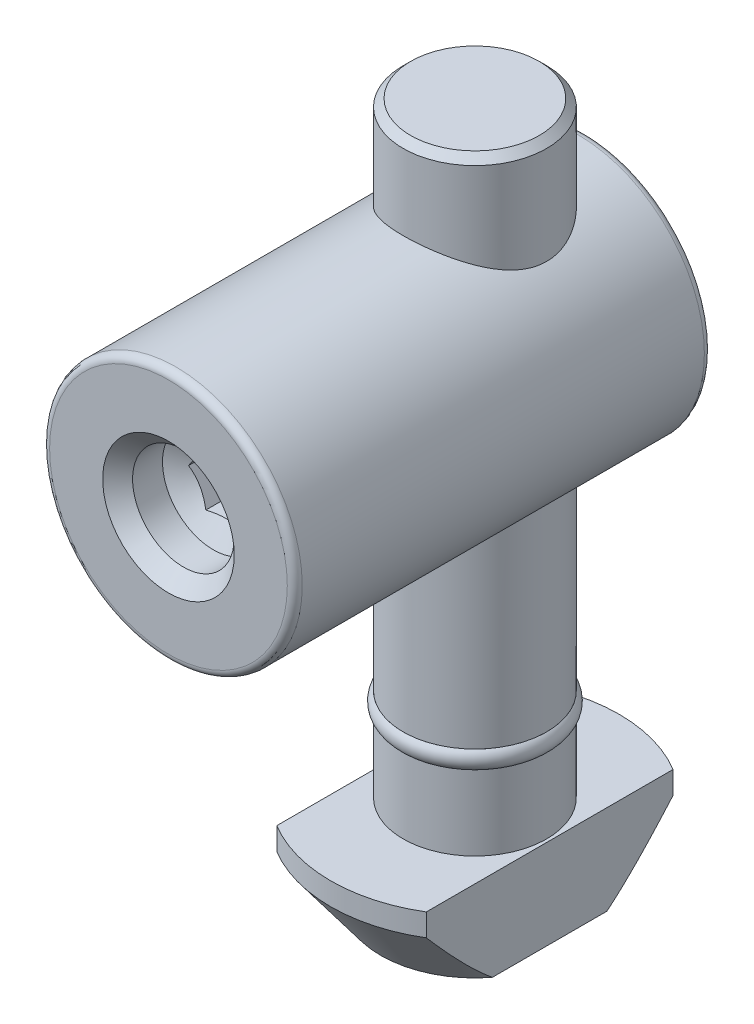
SolidWorks part; units mm, degrees
ref_plane "Спереди" through (0, 0, 0) normal (0, 0, 1) x (1, 0, 0)
ref_plane "Сверху" through (0, 0, 0) normal (0, 1, 0) x (1, 0, 0)
ref_plane "Справа" through (0, 0, 0) normal (1, 0, 0) x (0, 0, -1)
sketch "Эскиз3" plane through (0, 0, 0) normal (0, 0, 1) x (1, 0, 0)
  line L0 (0, 0) -> (-4.8, 0)
  line L1 (-4.8, 0) -> (-4.8, -34.3)
  line L2 (-4.8, -34.3) -> (-4.3, -34.3)
  line L3 (-4.3, -34.3) -> (-4.3, -35.5)
  line L4 (-4.3, -35.5) -> (-4.8, -35.5)
  line L5 (-4.8, -35.5) -> (-4.8, -40.5)
  line L7 (0, -46.5) -> (0, 0)
  line L8 (0, 0) -> (0, 5.384) construction
  line L9 (-4.8, -40.5) -> (-9.65, -40.5)
  line L10 (-9.65, -40.5) -> (-9.65, -42)
  line L11 (-9.65, -42) -> (-6.3, -46.5)
  line L12 (-6.3, -46.5) -> (0, -46.5)
  point P3 (0, -29.8286)
  point P9 (-4.2202, -32)
  dimension "D1" = 9.6
  dimension "D2" = 1.2
  dimension "D3" = 46.5
  dimension "D4" = 0.5
  dimension "D5" = 5
  dimension "D6" = 6
  dimension "D7" = 1.5
  dimension "D8" = 1.5
  dimension "D9" = 19.3
revolve "Повернуть1" add sketch "Эскиз3" angle 360 about L8
sketch "Эскиз6" plane through (0, -46.5, 0) normal (0, -1, 0) x (1, 0, 0)
  line L1 (-5, -9.65) -> (5, -9.65)
  line L2 (-5, -9.65) -> (-5, 9.65)
  line L3 (-5, 9.65) -> (5, 9.65)
  line L4 (5, -9.65) -> (5, 9.65)
  line L5 (-5, -9.65) -> (5, 9.65) construction
  line L6 (-5, 9.65) -> (5, -9.65) construction
  circle A1 centre (0, 0) radius 9.65 construction
  point P0 (0, 0)
  dimension "D1" = 10
extrude "Вырез-Вытянуть1" cut sketch "Эскиз6" against normal up to surface (6 mm away) flip side to cut up to face at (0, -40.5, -9.65)
chamfer "Фаска1" distance 0.5 angle 45 1 edges at (0, 0, -4.8)
sketch "Эскиз12" plane through (0, 0, 0) normal (0, 0, 1) x (1, 0, 0)
  line L0 (4.3, 0) -> (-4.3, 0) construction
  circle A0 centre (0, -14) radius 8.45
  point P4 (1.0261, -9)
  dimension "D1" = 16.9
  dimension "D2" = 14
extrude "Бобышка-Вытянуть2" add sketch "Эскиз12" along normal blind 20.5 and the other way blind 7.4
hole_wizard "Отверстие обработанное метчиком M81" positions "Эскиз13" profile "Эскиз14" tap size "M8" standard "ISO"
sketch "Эскиз13" plane through (0, 0, 20.5) normal (0, 0, 1) x (1, 0, 0)
  point P0 (0, -14)
cosmetic thread "Отверстие резьбы1" parameters "D1"=3, "D2"=8
sketch "Эскиз14" plane through (0, -14, 20.5) normal (1, 0, 0) x (0, -1, 0)
  line L0 (0, 0) -> (0, 5.0429)
  line L1 (0, 5.0429) -> (3.4, 3)
  line L2 (3.4, 3) -> (3.4, 1)
  line L3 (3.4, 1) -> (4.4, 0)
  line L5 (4.4, 0) -> (0, 0)
  line L6 (-3.4, 1) -> (-4.4, 0) construction
  line L10 (0, 5.0429) -> (-3.4, 3) construction
  line L11 (0, -6.35) -> (0, 107.95) construction
  dimension "Диаметр сверла" = 6.8
  dimension "Глубина сверла" = 3
  dimension "Диаметр передней зенковки" = 8.8
  dimension "Угол передней зенковки" = 90
  dimension "Угол заточки сверла" = 118
fillet "Скругление1" radius 0.5 2 edges at (8.45, -14, -7.4) (8.45, -14, 20.5)
sketch "Эскиз15" plane through (0, 0, 20.5) normal (0, 0, 1) x (1, 0, 0)
  line L1 (2.3094, -14) -> (1.1547, -12)
  line L2 (1.1547, -12) -> (-1.1547, -12)
  line L3 (-1.1547, -12) -> (-2.3094, -14)
  line L4 (-2.3094, -14) -> (-1.1547, -16)
  line L5 (-1.1547, -16) -> (1.1547, -16)
  line L6 (1.1547, -16) -> (2.3094, -14)
  circle A0 centre (0, -14) radius 2 construction
  dimension "D1" = 4
extrude "Вырез-Вытянуть2" cut sketch "Эскиз15" against normal blind 6
sketch "Эскиз16" plane through (0, 0, 0) normal (0, 0, 1) x (1, 0, 0)
  line L0 (-4.3, -34.3) -> (-4.8, -34.3)
  line L1 (-4.3, -34.3) -> (-4.3, -35.5) construction
  line L2 (-4.8, -35.5) -> (-4.3, -35.5)
  line L3 (-4.3, -35.5) -> (-4.3, -34.3)
  line L4 (-4.3, -34.3) -> (4.3, -34.3) construction
  line L7 (-4.8, -20.9543) -> (-4.8, -34.3) construction
  line L8 (4.8, -35.5) -> (-4.8, -35.5) construction
  line L9 (0, -34.3) -> (0, -35.5) construction
  arc A0 (-4.8, -34.3) -> (-4.8, -35.5) centre (-4.3, -34.9) ccw
  point P15 (-4.3, -34.9)
revolve "Повернуть2" add sketch "Эскиз16" angle 360 about L9
